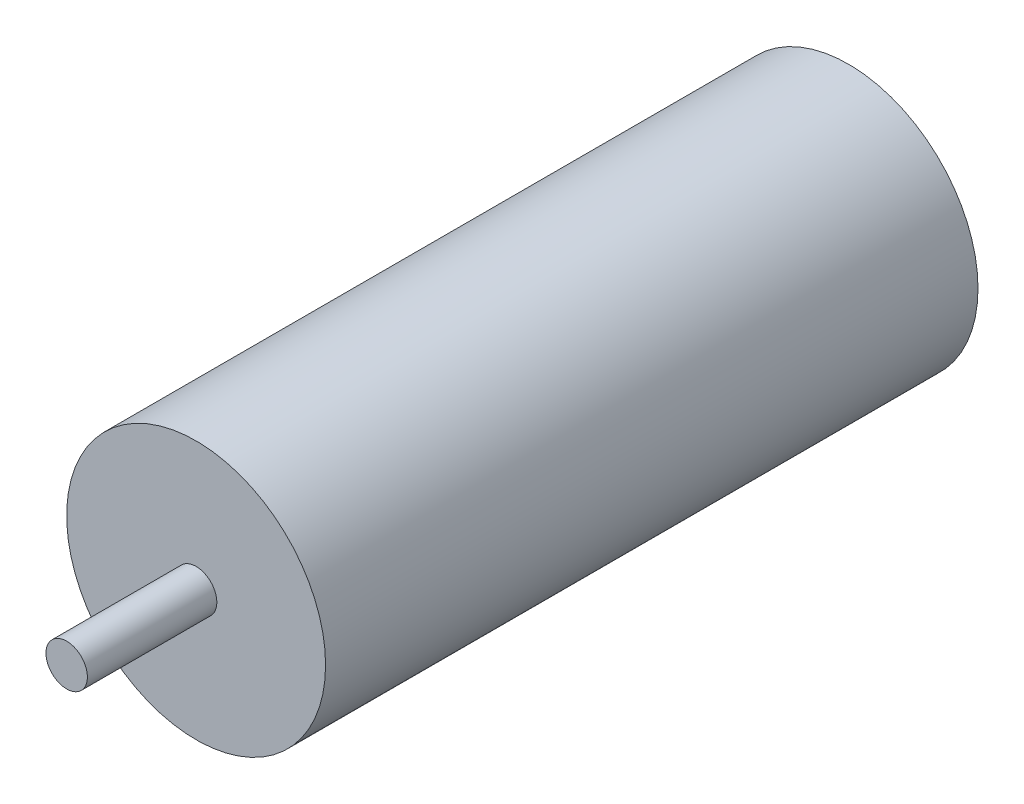
SolidWorks part; units mm, degrees
ref_plane "Front Plane" through (0, 0, 0) normal (0, 0, 1) x (1, 0, 0)
ref_plane "Top Plane" through (0, 0, 0) normal (0, 1, 0) x (1, 0, 0)
ref_plane "Right Plane" through (0, 0, 0) normal (1, 0, 0) x (0, 0, -1)
sketch "Sketch1" plane through (0, 0, 0) normal (0, 0, 1) x (1, 0, 0)
  circle A0 centre (0, 0) radius 12.5
  dimension "D1" = 25
extrude "Boss-Extrude1" add sketch "Sketch1" along normal blind 63
sketch "Sketch2" plane through (0, 0, 63) normal (0, 0, 1) x (1, 0, 0)
  circle A0 centre (0, 0) radius 2
  dimension "D1" = 4
extrude "Boss-Extrude2" add sketch "Sketch2" along normal blind 12.5
